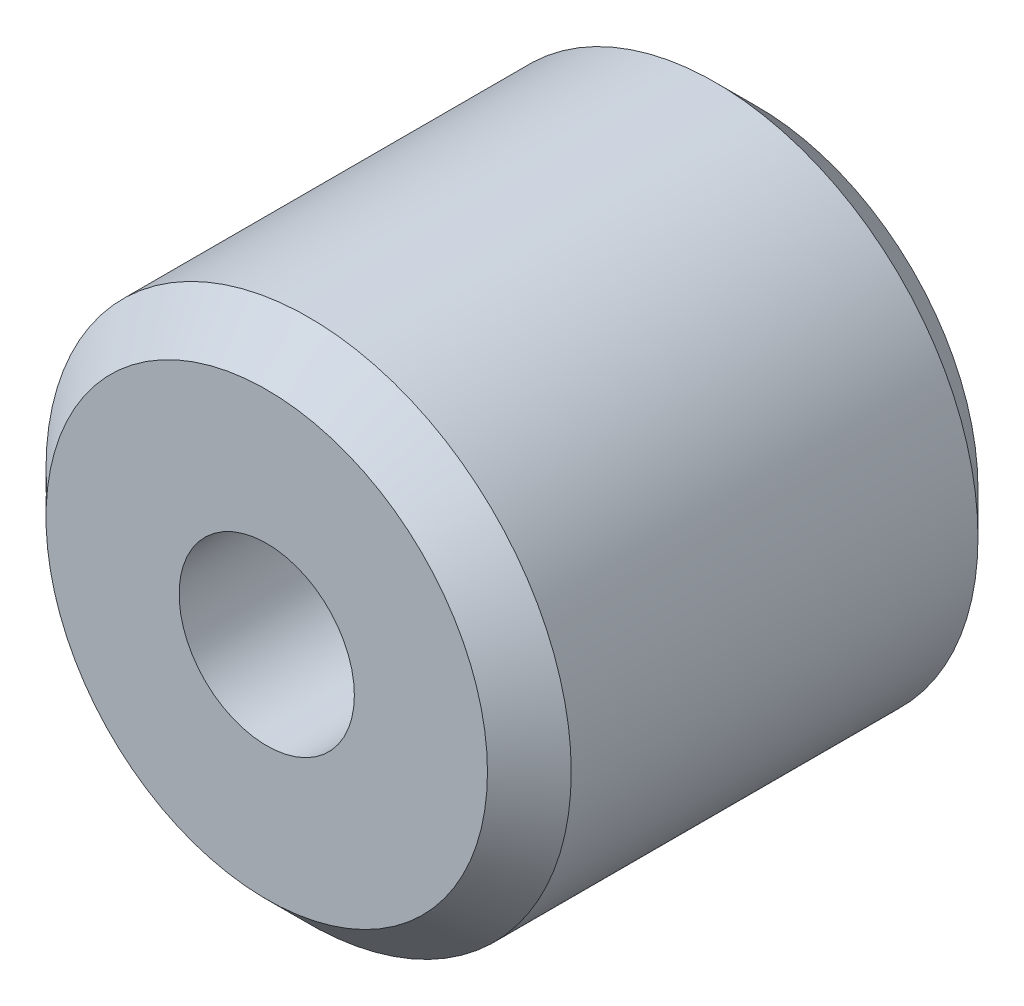
SolidWorks part; units mm, degrees
ref_plane "Front Plane" through (0, 0, 0) normal (0, 0, 1) x (1, 0, 0)
ref_plane "Top Plane" through (0, 0, 0) normal (0, 1, 0) x (1, 0, 0)
ref_plane "Right Plane" through (0, 0, 0) normal (1, 0, 0) x (0, 0, -1)
sketch "Sketch1" plane through (0, 0, 0) normal (0, 0, 1) x (1, 0, 0)
  circle A0 centre (0, 0) radius 4.765
  circle A1 centre (0, 0) radius 1.59
  dimension "D1" = 9.53
  dimension "D2" = 3.18
extrude "Boss-Extrude1" add sketch "Sketch1" along normal mid plane 8.9
chamfer "Chamfer1" distance 0.76 angle 45 2 edges at (4.765, 0, 4.45) (4.765, 0, -4.45)
